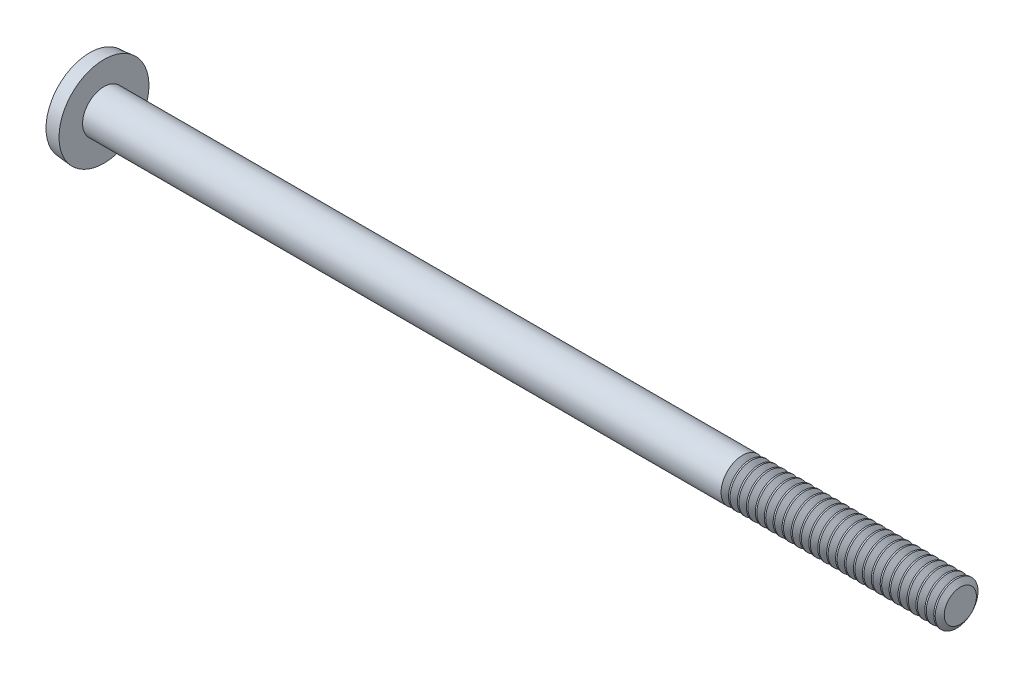
SolidWorks part; units mm, degrees
ref_plane "Plane1" through (0, 0, 0) normal (0, 0, 1) x (1, 0, 0)
ref_plane "Plane2" through (0, 0, 0) normal (0, 1, 0) x (1, 0, 0)
ref_plane "Plane3" through (0, 0, 0) normal (1, 0, 0) x (0, 0, -1)
sketch "BodySke" plane through (0, 0, 0) normal (0, 0, 1) x (1, 0, 0)
  line L0 (0.8128, 0.762) -> (0.8128, 1.6002)
  line L1 (0.8128, 1.6002) -> (0.3048, 1.5558)
  line L2 (-25.4, 0) -> (127, 0) construction
  line L3 (0.8128, -1.6002) -> (0.3048, -1.5558) construction
  line L4 (0.8128, 0.762) -> (31.2928, 0.762)
  line L5 (31.2928, 0.762) -> (31.2928, 0)
  line L6 (31.2928, 0) -> (0, 0)
  line L7 (0.8128, -0.762) -> (31.2928, -0.762) construction
  line L8 (1.1303, 6.35) -> (1.1303, -3.175) construction
  line L9 (23.6728, 6.35) -> (23.6728, -3.175) construction
  arc A0 (0, 0) -> (0.3048, 1.5558) centre (4.1228, 0) cw
  dimension "Head_ang" = 85
  dimension "Oval_ht" = 0.3048
  dimension "Head_ht" = 0.8128
  dimension "Diameter" = 1.524
  dimension "Length" = 30.48
  dimension "Head_dia" = 3.2004
  dimension "Advance" = 0.3175
  dimension "Thread_nom" = 7.62
revolve "Base-Revolve" add sketch "BodySke" angle 360 about L2
cosmetic thread "ThreadCosmetic" [suppressed] parameters "Thread_length"=7.62, "Thread_minor"=1.1455
sketch "Sketch2" plane through (0, 0, 0) normal (1, 0, 0) x (0, 0, -1)
  line L0 (1.6002, -0.2921) -> (1.6002, 0.2921)
  line L1 (1.6002, 0.2921) -> (-1.6002, 0.2921)
  line L2 (-1.6002, 0.2921) -> (-1.6002, -0.2921)
  line L3 (-1.6002, -0.2921) -> (1.6002, -0.2921)
  dimension "D1" = 3.2004
  dimension "D2" = 1.6002
  dimension "D3" = 0.2921
  dimension "Slot_width" = 0.5842
extrude "Slot" [suppressed] cut sketch "Sketch2" along normal blind 0.4572
sketch "Sketch3" plane through (0, 0, 0) normal (1, 0, 0) x (0, 0, -1)
  line L0 (-0.2921, 1.0541) -> (0.2921, 1.0541)
  line L1 (0.2921, 1.0541) -> (0.2921, -1.0541)
  line L2 (0.2921, -1.0541) -> (-0.2921, -1.0541)
  line L3 (-0.2921, -1.0541) -> (-0.2921, 1.0541)
  dimension "D1" = 0.2921
  dimension "Cross_width" = 0.5842
  dimension "D2" = 1.0541
  dimension "Cross_dia" = 2.1082
ref_plane "Plane4" through (1.0668, 0, 0) normal (1, 0, 0) x (0, 0, -1)
sketch "Sketch4" plane through (1.0668, 0, 0) normal (1, 0, 0) x (0, 0, -1)
  line L0 (-0.1461, 0.1461) -> (0.1461, 0.1461)
  line L1 (0.1461, 0.1461) -> (0.1461, -0.1461)
  line L2 (0.1461, -0.1461) -> (-0.1461, -0.1461)
  line L3 (-0.1461, -0.1461) -> (-0.1461, 0.1461)
  dimension "D1" = 0.2921
  dimension "D2" = 0.1461
  dimension "D3" = 0.2921
  dimension "D4" = 0.1461
loft "Cross" cut profiles "Sketch3", "Sketch4"
pattern_circular "CirPattern1" count 2 every 90 about axis through (0, 0, 0) along (1, 0, 0) of "Cross"
sketch "ThdSchSke" plane through (0, 0, 0) normal (0, 0, 1) x (1, 0, 0)
  line L0 (23.6728, -0.5728) -> (23.5403, -0.762)
  line L1 (23.6728, -0.5728) -> (23.8053, -0.762)
  line L2 (23.8053, -0.762) -> (23.8053, -0.9525)
  line L3 (-3.175, 0) -> (5.1513, 0) construction
  line L5 (23.8053, -0.9525) -> (23.5403, -0.9525)
  line L6 (23.5403, -0.9525) -> (23.5403, -0.762)
  dimension "Thread_minor" = 1.1455
  dimension "Diameter" = 1.524
  dimension "Start" = 23.6728
  dimension "SideAngle" = 55
  dimension "VeeAngle" = 70
  dimension "Overcut" = 1.905
revolve "ThreadSchematic" cut sketch "ThdSchSke" angle 360 about L3
pattern_linear "ThdSchPat" count 25 spacing 0.3175 along (1, 0, 0) of "ThreadSchematic"
equation "\"D1@Sketch3\" = \"Cross_width@Sketch3\" / 2"
equation "\"D2@Sketch3\" = \"Cross_dia@Sketch3\" / 2"
equation "\"D1@Sketch4\" = \"Cross_width@Sketch3\"*.5"
equation "\"D2@Sketch4\" = \"D1@Sketch4\" / 2"
equation "\"D3@Sketch4\" = \"D1@Sketch4\""
equation "\"D4@Sketch4\" = \"D2@Sketch4\""
equation "\"D1@Sketch2\" = \"Head_dia@BodySke\""
equation "\"D2@Sketch2\" = \"D1@Sketch2\" / 2"
equation "\"D3@Sketch2\" = \"Slot_width@Sketch2\" / 2"
equation "\"Thread_length@ThreadCosmetic\" = ((sgn( (\"Length@BodySke\" - \"Advance@BodySke\" ) - \"Thread_nom@BodySke\" )-1)*( (\"Length@BodySke\" - \"Advance@BodySke\" ) - \"Thread_nom@BodySke\" ))/-2+ \"Thread_nom@BodySke\""
equation "\"Thread_minor@ThdSchSke\" = \"Thread_minor@ThreadCosmetic\""
equation "\"Diameter@ThdSchSke\" = \"Diameter@BodySke\""
equation "\"Overcut@ThdSchSke\" = \"Diameter@BodySke\" * 1.25"
equation "\"Start@ThdSchSke\" = \"Head_ht@BodySke\" + \"Length@BodySke\" - \"Thread_length@ThreadCosmetic\"  '---Non-countersunk---"
equation "\"Num_threads@ThdSchPat\" = int( \"Thread_length@ThreadCosmetic\" / \"Advance@BodySke\" + 0.999 )  + 1"
equation "\"Advance@ThdSchPat\" = \"Thread_length@ThreadCosmetic\" /  (\"Num_threads@ThdSchPat\" - 1) 'relax it"
